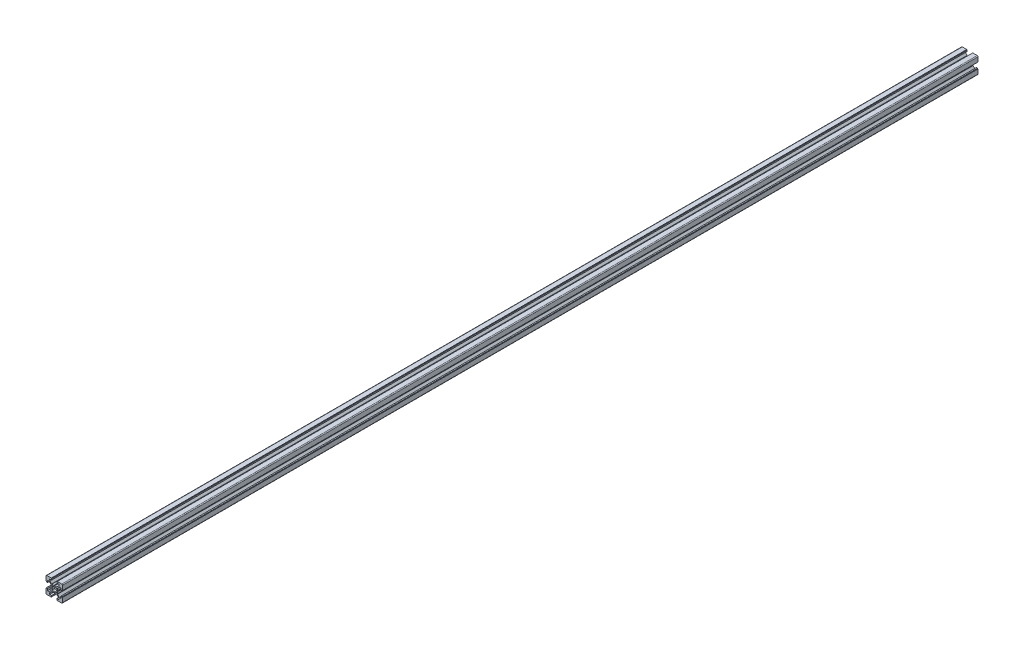
SolidWorks part; units mm, degrees
ref_plane "Спереди" through (0, 0, 0) normal (0, 0, 1) x (1, 0, 0)
ref_plane "Сверху" through (0, 0, 0) normal (0, 1, 0) x (1, 0, 0)
ref_plane "Справа" through (0, 0, 0) normal (1, 0, 0) x (0, 0, -1)
sketch "Sketch1" plane through (0, 0, 0) normal (0, 0, 1) x (1, 0, 0)
  line L0 (0, 10) -> (0, -10) construction
  line L1 (-10, -10) -> (10, -10) construction
  line L2 (-10, -10) -> (-10, 10) construction
  line L3 (-10, 10) -> (10, 10) construction
  line L4 (10, -10) -> (10, 10) construction
  line L5 (-10, -10) -> (10, 10) construction
  line L6 (-10, 10) -> (10, -10) construction
  line L7 (-10, 0) -> (10, 0) construction
  line L8 (0, 3.9) -> (-2.8444, 3.9)
  line L9 (-3.1979, 4.0464) -> (-5.5, 6.3485)
  line L10 (-5.5, 6.3485) -> (-5.5, 8.1)
  line L11 (-5.5, 8.1) -> (-3.1, 8.1)
  line L12 (-3.1, 8.1) -> (-3.1, 9.5)
  line L13 (-3.1, 9.5) -> (-3.4, 9.5)
  line L14 (-3.6, 9.7) -> (-3.6, 10)
  line L15 (-3.6, 10) -> (-9, 10)
  line L16 (-10, 3.6) -> (-10, 9)
  line L17 (-9.7, 3.6) -> (-10, 3.6)
  line L18 (-9.5, 3.1) -> (-9.5, 3.4)
  line L19 (-8.1, 3.1) -> (-9.5, 3.1)
  line L20 (-8.1, 5.5) -> (-8.1, 3.1)
  line L21 (-6.3485, 5.5) -> (-8.1, 5.5)
  line L22 (-4.0464, 3.1979) -> (-6.3485, 5.5)
  line L23 (-3.9, 0) -> (-3.9, 2.8444)
  line L24 (3.9, 0) -> (3.9, 2.8444)
  line L25 (4.0464, 3.1979) -> (6.3485, 5.5)
  line L26 (6.3485, 5.5) -> (8.1, 5.5)
  line L27 (8.1, 5.5) -> (8.1, 3.1)
  line L28 (8.1, 3.1) -> (9.5, 3.1)
  line L29 (9.5, 3.1) -> (9.5, 3.4)
  line L30 (9.7, 3.6) -> (10, 3.6)
  line L31 (10, 3.6) -> (10, 9)
  line L32 (3.6, 10) -> (9, 10)
  line L33 (3.6, 9.7) -> (3.6, 10)
  line L34 (3.1, 9.5) -> (3.4, 9.5)
  line L35 (3.1, 8.1) -> (3.1, 9.5)
  line L36 (5.5, 8.1) -> (3.1, 8.1)
  line L37 (5.5, 6.3485) -> (5.5, 8.1)
  line L38 (3.1979, 4.0464) -> (5.5, 6.3485)
  line L39 (0, 3.9) -> (2.8444, 3.9)
  line L40 (0, -3.9) -> (2.8444, -3.9)
  line L41 (3.1979, -4.0464) -> (5.5, -6.3485)
  line L42 (5.5, -6.3485) -> (5.5, -8.1)
  line L43 (5.5, -8.1) -> (3.1, -8.1)
  line L44 (3.1, -8.1) -> (3.1, -9.5)
  line L45 (3.1, -9.5) -> (3.4, -9.5)
  line L46 (3.6, -9.7) -> (3.6, -10)
  line L47 (3.6, -10) -> (9, -10)
  line L48 (10, -3.6) -> (10, -9)
  line L49 (9.7, -3.6) -> (10, -3.6)
  line L50 (9.5, -3.1) -> (9.5, -3.4)
  line L51 (8.1, -3.1) -> (9.5, -3.1)
  line L52 (8.1, -5.5) -> (8.1, -3.1)
  line L53 (6.3485, -5.5) -> (8.1, -5.5)
  line L54 (4.0464, -3.1979) -> (6.3485, -5.5)
  line L55 (3.9, 0) -> (3.9, -2.8444)
  line L56 (-3.9, 0) -> (-3.9, -2.8444)
  line L57 (-4.0464, -3.1979) -> (-6.3485, -5.5)
  line L58 (-6.3485, -5.5) -> (-8.1, -5.5)
  line L59 (-8.1, -5.5) -> (-8.1, -3.1)
  line L60 (-8.1, -3.1) -> (-9.5, -3.1)
  line L61 (-9.5, -3.1) -> (-9.5, -3.4)
  line L62 (-9.7, -3.6) -> (-10, -3.6)
  line L63 (-10, -3.6) -> (-10, -9)
  line L64 (-3.6, -10) -> (-9, -10)
  line L65 (-3.6, -9.7) -> (-3.6, -10)
  line L66 (-3.1, -9.5) -> (-3.4, -9.5)
  line L67 (-3.1, -8.1) -> (-3.1, -9.5)
  line L68 (-5.5, -8.1) -> (-3.1, -8.1)
  line L69 (-5.5, -6.3485) -> (-5.5, -8.1)
  line L70 (-3.1979, -4.0464) -> (-5.5, -6.3485)
  line L71 (0, -3.9) -> (-2.8444, -3.9)
  line L72 (2.0856, -1.3785) -> (2.8284, -2.1213)
  line L73 (2.0856, 1.3785) -> (2.8284, 2.1213)
  line L74 (2.8284, 2.1213) -> (2.1213, 2.8284)
  line L75 (2.1213, -2.8284) -> (2.8284, -2.1213)
  line L76 (1.3785, -2.0856) -> (2.1213, -2.8284)
  line L77 (1.3785, 2.0856) -> (2.1213, 2.8284)
  line L78 (-1.3785, -2.0856) -> (-2.1213, -2.8284)
  line L79 (-2.8284, -2.1213) -> (-2.1213, -2.8284)
  line L80 (-2.0856, -1.3785) -> (-2.8284, -2.1213)
  line L81 (-2.0856, 1.3785) -> (-2.8284, 2.1213)
  line L82 (-2.1213, 2.8284) -> (-2.8284, 2.1213)
  line L83 (-1.3785, 2.0856) -> (-2.1213, 2.8284)
  line L84 (-0.5, 3.9) -> (0, 3.4)
  line L85 (0, 3.4) -> (0.5, 3.9)
  line L86 (3.9, 0.5) -> (3.4, 0)
  line L87 (3.4, 0) -> (3.9, -0.5)
  line L88 (0.5, -3.9) -> (0, -3.4)
  line L89 (0, -3.4) -> (-0.5, -3.9)
  line L90 (-3.9, -0.5) -> (-3.4, 0)
  line L91 (-3.4, 0) -> (-3.9, 0.5)
  circle A0 centre (0, 0) radius 2.5
  arc A1 (-9, 10) -> (-10, 9) centre (-9, 9) ccw
  arc A2 (-2.8444, 3.9) -> (-3.1979, 4.0464) centre (-2.8444, 4.4) cw
  arc A3 (-3.4, 9.5) -> (-3.6, 9.7) centre (-3.4, 9.7) cw
  arc A4 (-9.5, 3.4) -> (-9.7, 3.6) centre (-9.7, 3.4) ccw
  arc A5 (-3.9, 2.8444) -> (-4.0464, 3.1979) centre (-4.4, 2.8444) ccw
  arc A6 (10, 9) -> (9, 10) centre (9, 9) ccw
  arc A7 (3.9, 2.8444) -> (4.0464, 3.1979) centre (4.4, 2.8444) cw
  arc A8 (9.5, 3.4) -> (9.7, 3.6) centre (9.7, 3.4) cw
  arc A9 (3.4, 9.5) -> (3.6, 9.7) centre (3.4, 9.7) ccw
  arc A10 (2.8444, 3.9) -> (3.1979, 4.0464) centre (2.8444, 4.4) ccw
  arc A11 (9, -10) -> (10, -9) centre (9, -9) ccw
  arc A12 (2.8444, -3.9) -> (3.1979, -4.0464) centre (2.8444, -4.4) cw
  arc A13 (3.4, -9.5) -> (3.6, -9.7) centre (3.4, -9.7) cw
  arc A14 (9.5, -3.4) -> (9.7, -3.6) centre (9.7, -3.4) ccw
  arc A15 (3.9, -2.8444) -> (4.0464, -3.1979) centre (4.4, -2.8444) ccw
  arc A16 (-10, -9) -> (-9, -10) centre (-9, -9) ccw
  arc A17 (-3.9, -2.8444) -> (-4.0464, -3.1979) centre (-4.4, -2.8444) cw
  arc A18 (-9.5, -3.4) -> (-9.7, -3.6) centre (-9.7, -3.4) cw
  arc A19 (-3.4, -9.5) -> (-3.6, -9.7) centre (-3.4, -9.7) ccw
  arc A20 (-2.8444, -3.9) -> (-3.1979, -4.0464) centre (-2.8444, -4.4) ccw
  point P0 (0, 0)
  point P42 (0, 0)
  point P70 (0, 0)
  point P98 (0, 0)
  point P126 (0, 0)
  point P139 (0, 0)
  point P152 (0, 0)
  dimension "D3" = 5
  dimension "D4" = 2
  dimension "D12" = 0.5
  dimension "D13" = 0.2
  dimension "D15" = 1
  dimension "D1" = 20
  dimension "D2" = 20
  dimension "D5" = 6.2
  dimension "D6" = 7.2
  dimension "D7" = 1.9
  dimension "D8" = 0.5
  dimension "D10" = 1.2
  dimension "D11" = 6.1
  dimension "D16" = 3.5
  dimension "D18" = 0.5
  dimension "D14" = 4
  dimension "D17" = 4
  dimension "D19" = 4
extrude "Extrude1" add sketch "Sketch1" along normal blind 1110 contours A20 L71 L89 L88 L40 A12 L41 L42 L43 L44 L45 A13 L46 L47 A11 L48 L49 A14 L50 L51 L52 L53 L54 A15 L55 L87 L86 L24 A7 L25 L26 L27 L28 L29 A8 L30 L31 A6 L32 L33 A9 L34 L35 L36 L37 L38 A10 L39 L85 L84 L8
